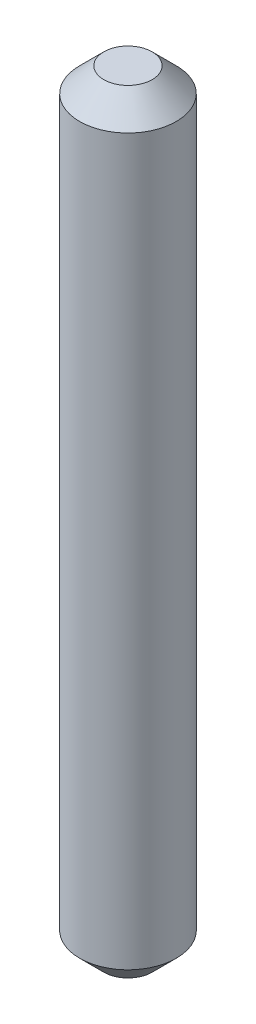
SolidWorks part; units mm, degrees
ref_plane "Front Plane" through (0, 0, 0) normal (0, 0, 1) x (1, 0, 0)
ref_plane "Top Plane" through (0, 0, 0) normal (0, 1, 0) x (1, 0, 0)
ref_plane "Right Plane" through (0, 0, 0) normal (1, 0, 0) x (0, 0, -1)
sketch "Sketch1" plane through (0, 0, 0) normal (0, 1, 0) x (1, 0, 0)
  circle A0 centre (0, 0) radius 0.5
  dimension "D1" = 1
extrude "Boss-Extrude1" add sketch "Sketch1" along normal blind 8
chamfer "Chamfer1" distance 0.25 angle 45 2 edges at (0, 0, 0.5) (0, 8, 0.5)
